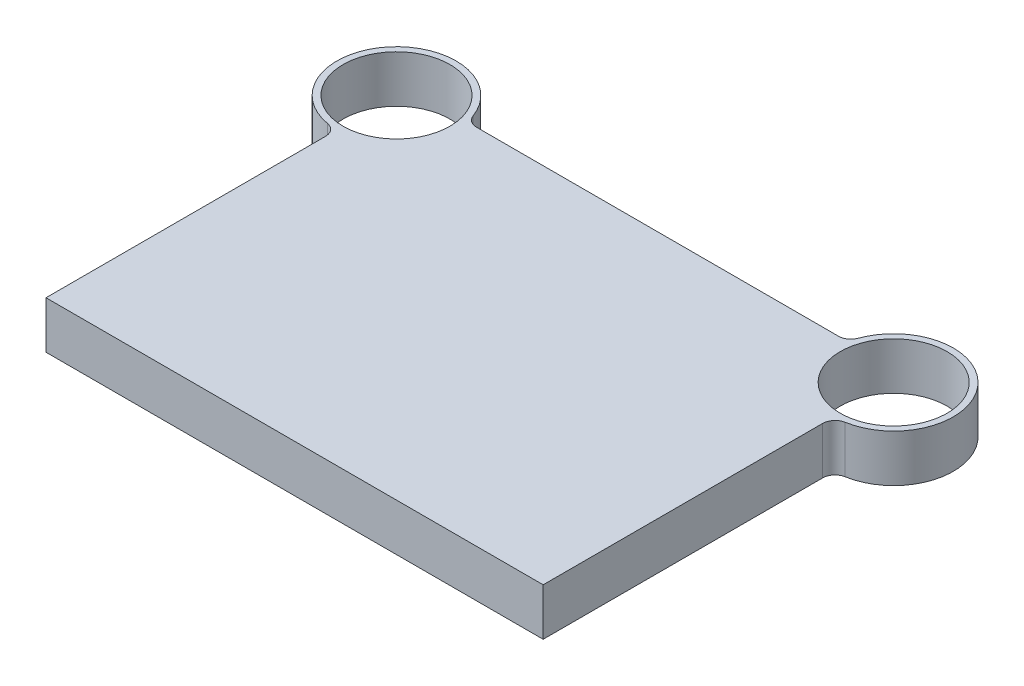
SolidWorks part; units mm, degrees
ref_plane "Front Plane" through (0, 0, 0) normal (0, 0, 1) x (1, 0, 0)
ref_plane "Top Plane" through (0, 0, 0) normal (0, 1, 0) x (1, 0, 0)
ref_plane "Right Plane" through (0, 0, 0) normal (1, 0, 0) x (0, 0, -1)
sketch "Sketch1" plane through (0, 0, 0) normal (0, 1, 0) x (1, 0, 0)
  line L0 (200, 0) -> (-200, 0)
  line L1 (-200, 0) -> (-200, 234)
  line L2 (0, 0) -> (0, 292) construction
  line L3 (153.0532, 292) -> (-153.0532, 292)
  line L4 (200, 0) -> (200, 234)
  arc A0 (-153.0532, 292) -> (-200, 234) centre (-200, 282) ccw
  circle A1 centre (-200, 282) radius 43
  circle A2 centre (200, 282) radius 43
  arc A3 (153.0532, 292) -> (200, 234) centre (200, 282) cw
  point P9 (-200, 167.2708)
  point P10 (-111.6663, 239.5025)
  dimension "D2" = 96
  dimension "D3" = 86
  dimension "D1" = 400
  dimension "D4" = 400
  dimension "D5" = 282
  dimension "D6" = 292
extrude "Boss-Extrude1" add sketch "Sketch1" along normal blind 38
fillet "Fillet1" radius 10 4 edges at (200, 19, -234) (153.0532, 19, -292) (-153.0532, 19, -292) (-200, 19, -234)
